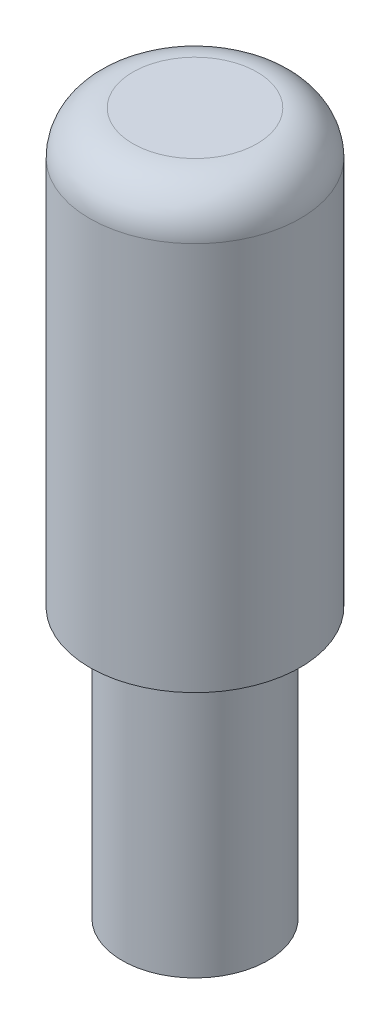
SolidWorks part; units mm, degrees
material "Ti-6Al-2Sn-2Zr-2Mo-2Cr-0.25Si (SS)"
ref_plane "Front Plane" through (0, 0, 0) normal (0, 0, 1) x (1, 0, 0)
ref_plane "Top Plane" through (0, 0, 0) normal (0, 1, 0) x (1, 0, 0)
ref_plane "Right Plane" through (0, 0, 0) normal (1, 0, 0) x (0, 0, -1)
sketch "Sketch1" plane through (0, 0, 0) normal (0, 1, 0) x (1, 0, 0)
  circle A0 centre (0, 0) radius 97.5
  dimension "D1" = 195
extrude "Boss-Extrude1" add sketch "Sketch1" along normal blind 650
sketch "Sketch2" plane through (0, 0, 0) normal (0, -1, 0) x (1, 0, 0)
  circle A0 centre (0, 0) radius 67.5
  circle A1 centre (0, 0) radius 97.5 construction
  circle A2 centre (0, 0) radius 97.5
  dimension "D1" = 30
  dimension "D2" = 195
extrude "Cut-Extrude4" cut sketch "Sketch2" against normal blind 250
sketch "Sketch4" plane through (0, 0, 0) normal (0, 0, 1) x (1, 0, 0)
  line L0 (0, 0) -> (0, 900) construction
  line L1 (97.5, 650) -> (-97.5, 650) construction
  circle A0 centre (0, 450) radius 67.5
  dimension "D1" = 135
  dimension "D2" = 200
extrude "Cut-Extrude3" cut sketch "Sketch4" against normal through all
fillet "Fillet1" radius 40 1 edges at (0, 650, 97.5)
